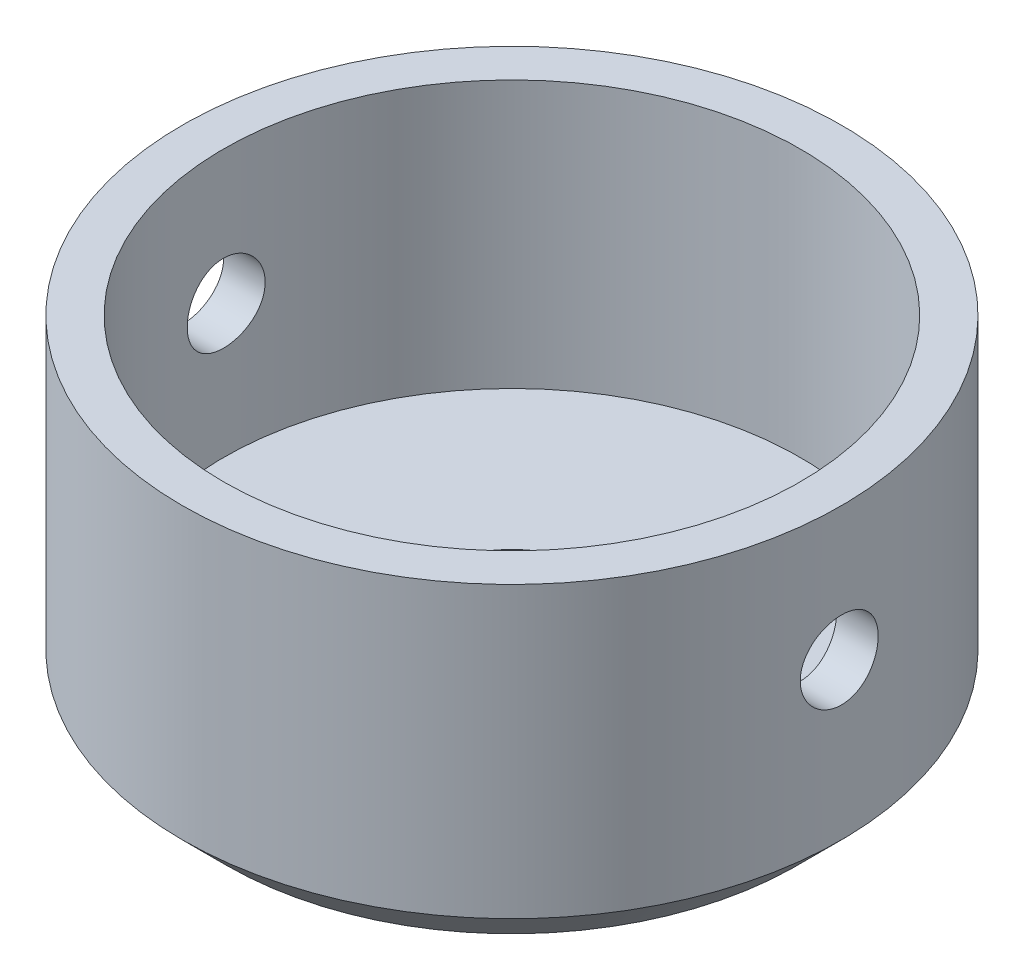
SolidWorks part; units mm, degrees
ref_plane "Front Plane" through (0, 0, 0) normal (0, 0, 1) x (1, 0, 0)
ref_plane "Top Plane" through (0, 0, 0) normal (0, 1, 0) x (1, 0, 0)
ref_plane "Right Plane" through (0, 0, 0) normal (1, 0, 0) x (0, 0, -1)
sketch "Sketch1" plane through (0, 0, 0) normal (0, 1, 0) x (1, 0, 0)
  circle A0 centre (0, 0) radius 12.8 construction
  circle A1 centre (0, 0) radius 14.8
  dimension "D1" = 25.6
  dimension "D2" = 2
extrude "Boss-Extrude1" add sketch "Sketch1" along normal blind 15
sketch "Sketch2" plane through (0, 15, 0) normal (0, 1, 0) x (1, 0, 0)
  circle A0 centre (0, 0) radius 12.95
  dimension "D1" = 25.9
extrude "Cut-Extrude1" cut sketch "Sketch2" against normal offset from surface (12 mm away) 3 up to face at (0, 0, 14.8)
sketch "Sketch3" plane through (0, 0, 0) normal (1, 0, 0) x (0, 0, -1)
  line L0 (0, 15) -> (0, 9) construction
  line L1 (12.95, 15) -> (-12.95, 15) construction
  circle A0 centre (0, 9) radius 1.75
  dimension "D2" = 3.5
  dimension "D1" = 6
extrude "Cut-Extrude2" cut sketch "Sketch3" against normal through all both and the other way through all
sketch "Sketch4" plane through (0, 0, 0) normal (0, -1, 0) x (1, 0, 0)
  circle A0 centre (0, 0) radius 4.1
  dimension "D1" = 8.2
extrude "Cut-Extrude3" cut sketch "Sketch4" against normal through all
chamfer "Chamfer1" distance 2 angle 45 1 edges at (0, 0, 14.8)
